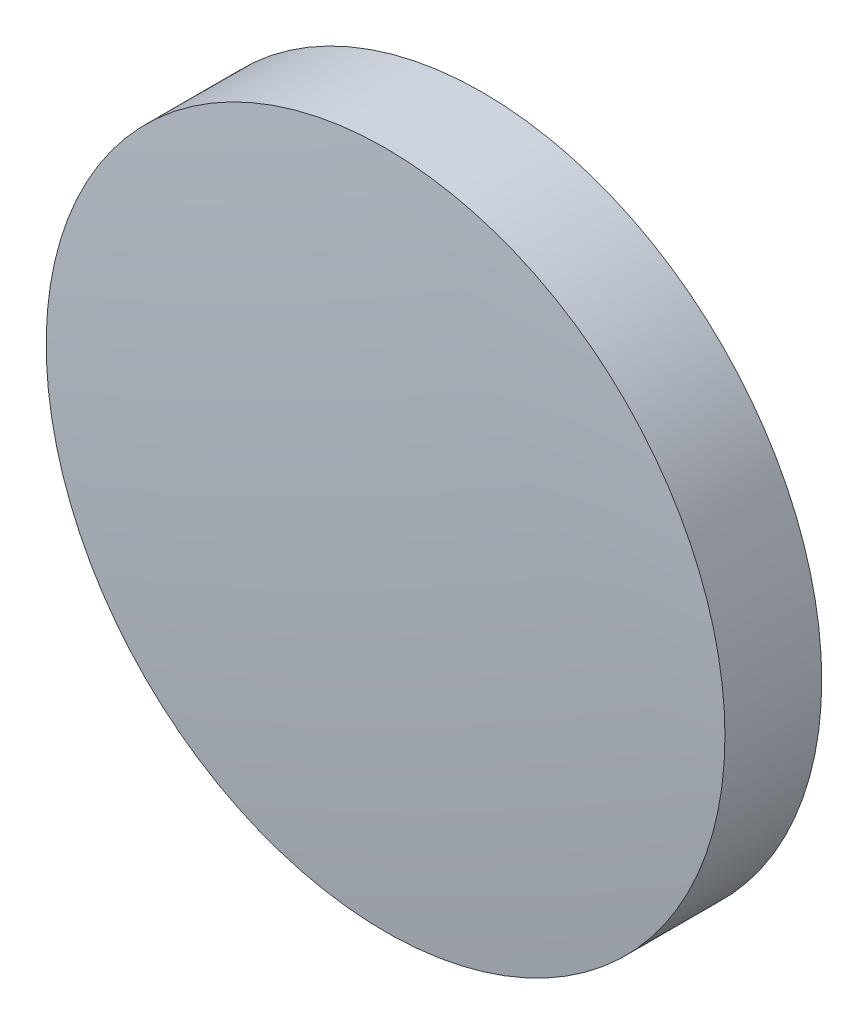
SolidWorks part; units mm, degrees
material "Glass"
ref_plane "Front Plane" through (0, 0, 0) normal (0, 0, 1) x (1, 0, 0)
ref_plane "Top Plane" through (0, 0, 0) normal (0, 1, 0) x (1, 0, 0)
ref_plane "Right Plane" through (0, 0, 0) normal (1, 0, 0) x (0, 0, -1)
sketch "Sketch2" plane through (0, 0, 0) normal (1, 0, 0) x (0, 0, -1)
  line L0 (-1.2, 0) -> (1.2, 0)
  line L1 (-0.9055, 6.35) -> (0.9055, 6.35)
  arc A0 (1.2, 0) -> (0.9055, 6.35) centre (-67.4, 0) ccw
  arc A1 (-1.2, 0) -> (-0.9055, 6.35) centre (67.4, 0) cw
  dimension "R2" = 68.6
  dimension "R1" = 68.6
  dimension "D1" = 6.35
  dimension "CT" = 2.4
revolve "Revolve1" add sketch "Sketch2" angle 360 about L0
